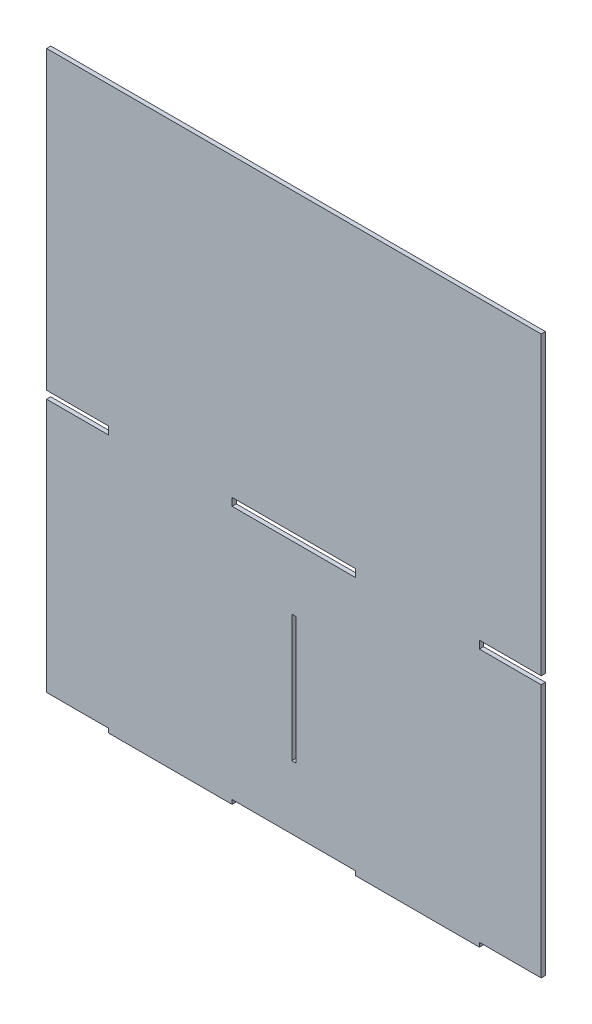
SolidWorks part; units mm, degrees
ref_plane "Plano frontal" through (0, 0, 0) normal (0, 0, 1) x (1, 0, 0)
ref_plane "Plano superior" through (0, 0, 0) normal (0, 1, 0) x (1, 0, 0)
ref_plane "Plano direito" through (0, 0, 0) normal (1, 0, 0) x (0, 0, -1)
sketch "Esboço1" plane through (0, 0, 0) normal (0, 0, 1) x (1, 0, 0)
  line L0 (-308.0713, 0) -> (-308.0713, -3)
  line L1 (0, 0) -> (-44.011, 0)
  line L2 (0, 0) -> (0, 180.7624)
  line L3 (0, 397) -> (-352.0815, 397)
  line L4 (-352.0815, 0) -> (-352.0815, 180.7624)
  line L5 (-308.0713, -3) -> (-220.051, -3)
  line L6 (-220.051, -3) -> (-220.051, 0)
  line L7 (-132.0313, 0) -> (-132.0313, -3)
  line L8 (-132.0313, -3) -> (-44.011, -3)
  line L9 (-44.011, -3) -> (-44.011, 0)
  line L10 (-308.0713, 0) -> (-352.0815, 0)
  line L11 (-132.0313, 0) -> (-220.051, 0)
  line L12 (-132.0306, 186.2624) -> (-44.0102, 186.2624) construction
  line L13 (-308.0713, 186.2624) -> (-220.051, 186.2624) construction
  line L14 (-308.0713, 186.2624) -> (-308.0713, 180.7624)
  line L15 (-308.0713, 180.7624) -> (-220.051, 180.7624) construction
  line L16 (-220.051, 186.2624) -> (-220.051, 180.7624)
  line L17 (-132.0306, 186.2624) -> (-132.0306, 180.7624)
  line L18 (-132.0306, 180.7624) -> (-44.0102, 180.7624) construction
  line L19 (-44.0102, 186.2624) -> (-44.0102, 180.7624)
  line L20 (-308.0713, 186.2624) -> (-352.0815, 186.2624)
  line L21 (-308.0713, 180.7624) -> (-352.0815, 180.7624)
  line L22 (-220.051, 186.2624) -> (-132.0306, 186.2624)
  line L23 (-220.051, 180.7624) -> (-132.0306, 180.7624)
  line L24 (-44.0102, 186.2624) -> (0, 186.2624)
  line L25 (-44.0102, 180.7624) -> (0, 180.7624)
  line L26 (-352.0815, 186.2624) -> (-352.0815, 397)
  line L27 (0, 186.2624) -> (0, 397)
  line L29 (-174.5408, 45.1906) -> (-177.5408, 45.1906)
  line L30 (-174.5408, 45.1906) -> (-174.5408, 135.5718)
  line L31 (-174.5408, 135.5718) -> (-177.5408, 135.5718)
  line L32 (-177.5408, 45.1906) -> (-177.5408, 135.5718)
  point P29 (-176.0408, 135.5718)
  point P30 (-176.0408, 180.7624)
  dimension "D1" = 352.0815
  dimension "D2" = 397
  dimension "D3" = 44.0102
  dimension "D4" = 88.0204
  dimension "D5" = 2
  dimension "D6" = 88.0196
  dimension "D7" = 3
  dimension "D8" = 180.7624
  dimension "D9" = 44.0102
  dimension "D10" = 5.5
  dimension "D11" = 88.0204
  dimension "D13" = 88.0204
  dimension "D14" = 90.3812
  dimension "D15" = 3
  dimension "D16" = 45.1906
  dimension "D12" = 2
extrude "Ressalto-extrusão1" add sketch "Esboço1" along normal blind 3
